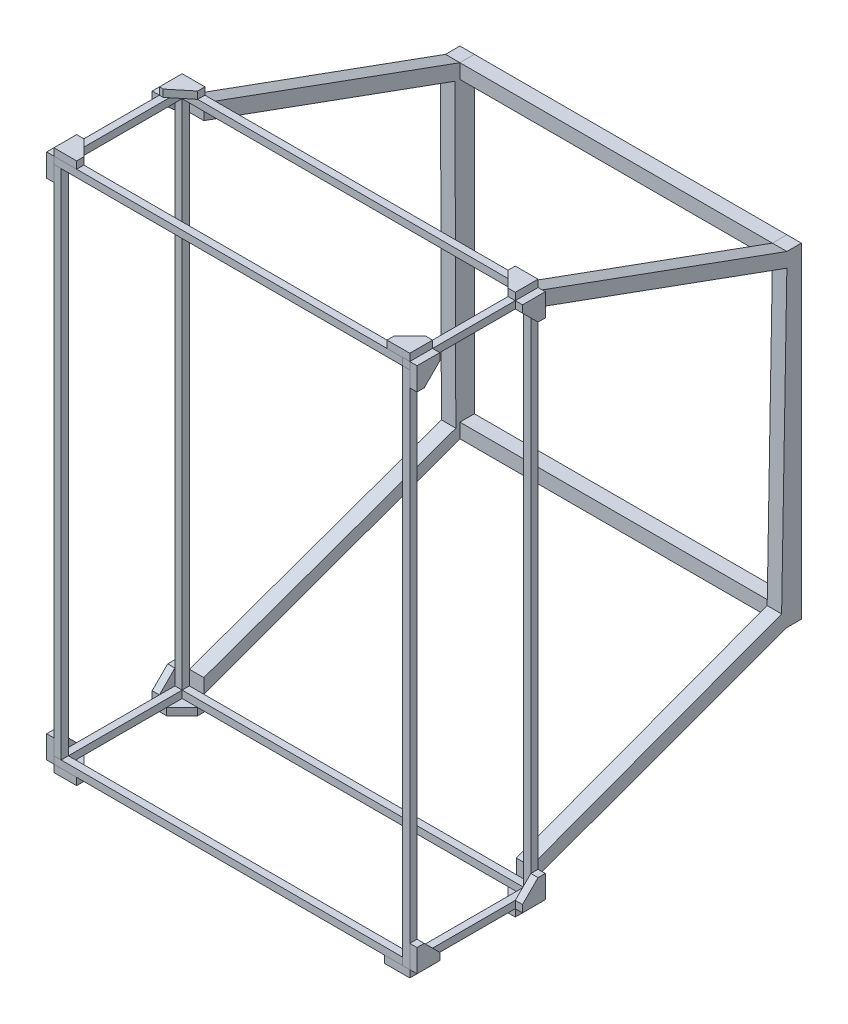
SolidWorks part; units mm, degrees
ref_plane "Front Plane" through (0, 0, 0) normal (0, 0, 1) x (1, 0, 0)
ref_plane "Top Plane" through (0, 0, 0) normal (0, 1, 0) x (1, 0, 0)
ref_plane "Right Plane" through (0, 0, 0) normal (1, 0, 0) x (0, 0, -1)
sketch "Sketch1" plane through (0, 0, 0) normal (0, 0, 1) x (1, 0, 0)
  line L1 (0, 0) -> (6.35, 0)
  line L2 (0, 0) -> (0, 6.35)
  line L3 (0, 6.35) -> (6.35, 6.35)
  line L4 (6.35, 0) -> (6.35, 6.35)
  dimension "D1" = 6.35
  dimension "D2" = 6.35
extrude "Boss-Extrude1" add sketch "Sketch1" along normal blind 100 contours L3 L4 L1 L2
ref_plane "Plane1" through (0, 0, 100) normal (1, 0, 0) x (0, 0, -1)
sketch "Sketch4" plane through (0, 0, 0) normal (0, -1, 0) x (-1, 0, 0)
  line L1 (0, -106.35) -> (-6.35, -106.35)
  line L2 (0, -106.35) -> (0, -100)
  line L3 (0, -100) -> (-6.35, -100)
  line L4 (-6.35, -106.35) -> (-6.35, -100)
  dimension "D1" = 6.35
extrude "Boss-Extrude3" add sketch "Sketch4" along normal blind 450 and the other way up to vertex (6.35 mm away) separate body contours L1 L4 L3 L2 other way up to point (0, 6.35, 100)
sketch "Sketch6" plane through (0, 0, 100) normal (0, 0, -1) x (-1, 0, 0)
  line L1 (-6.35, -450) -> (0, -450)
  line L2 (-6.35, -450) -> (-6.35, -456.3788)
  line L3 (-6.35, -456.3788) -> (0, -456.3788)
  line L4 (0, -450) -> (0, -456.3788)
extrude "Boss-Extrude4" add sketch "Sketch6" along normal blind 100 separate body contours L4 L3 L2 L1
sketch "Sketch7" plane through (6.35, 0, 0) normal (1, 0, 0) x (0, 0, -1)
  line L0 (-100, 0) -> (0, 0) construction
  line L1 (-106.35, 0) -> (-100, 0)
  line L2 (-106.35, 0) -> (-106.35, 6.35)
  line L3 (-106.35, 6.35) -> (-100, 6.35)
  line L4 (-100, 0) -> (-100, 6.35)
extrude "Boss-Extrude5" add sketch "Sketch7" along normal blind 300 and the other way up to vertex (6.35 mm away) separate body contours L3 L4 L1 L2 other way up to point (0, 6.35, 106.35)
sketch "Sketch8" plane through (6.35, 0, 0) normal (1, 0, 0) x (0, 0, -1)
  line L1 (-106.35, -450) -> (-100, -450)
  line L2 (-106.35, -450) -> (-106.35, -456.3788)
  line L3 (-106.35, -456.3788) -> (-100, -456.3788)
  line L4 (-100, -450) -> (-100, -456.3788)
extrude "Boss-Extrude6" add sketch "Sketch8" along normal blind 300 and the other way up to vertex (6.35 mm away) separate body other way up to point (0, -450, 106.35)
sketch "Sketch10" plane through (0, -450, 0) normal (0, 1, 0) x (1, 0, 0)
  line L1 (306.35, -100) -> (312.7, -100)
  line L2 (306.35, -100) -> (306.35, -106.35)
  line L3 (306.35, -106.35) -> (312.7, -106.35)
  line L4 (312.7, -100) -> (312.7, -106.35)
  dimension "D1" = 6.35
  dimension "D2" = 6.35
extrude "Boss-Extrude7" add sketch "Sketch10" along normal blind 450 and the other way up to vertex (6.3788 mm away) separate body contours L1 L4 L3 L2 other way up to point (306.35, -456.3788, 106.35)
sketch "Sketch12" plane through (0, 0, 0) normal (0, -1, 0) x (-1, 0, 0)
  line L1 (0, 0) -> (-6.35, 0)
  line L2 (0, 0) -> (0, 6.35)
  line L3 (0, 6.35) -> (-6.35, 6.35)
  line L4 (-6.35, 0) -> (-6.35, 6.35)
  dimension "D1" = 6.35
  dimension "D2" = 6.35
extrude "Boss-Extrude8" add sketch "Sketch12" along normal blind 450 and the other way up to vertex (6.35 mm away) separate body contours L2 L3 L4 L1 other way up to point (0, 6.35, 0)
sketch "Sketch16" plane through (0, 0, 100) normal (0, 0, -1) x (-1, 0, 0)
  line L1 (-306.35, -450) -> (-312.7, -450)
  line L2 (-306.35, -450) -> (-306.35, -456.35)
  line L3 (-306.35, -456.35) -> (-312.7, -456.35)
  line L4 (-312.7, -450) -> (-312.7, -456.35)
  line L5 (-306.35, 0) -> (-312.7, 0)
  line L6 (-306.35, 0) -> (-306.35, 6.4147)
  line L7 (-306.35, 6.4147) -> (-312.7, 6.4147)
  line L8 (-312.7, 0) -> (-312.7, 6.4147)
  dimension "D1" = 6.35
  dimension "D2" = 6.35
extrude "Boss-Extrude9" add sketch "Sketch16" along normal blind 100 separate body contours L3 L4 L1 L2
ref_plane "Plane2" through (312.7, 0, 100) normal (1, 0, 0) x (0, 0, -1)
ref_plane "Plane3" through (312.7, 0, 100) normal (0, -1, 0) x (-1, 0, 0)
sketch "Sketch20" plane through (0, 0, 100) normal (0, 0, -1) x (-1, 0, 0)
  line L0 (-436.45, 0) -> (-188.95, 0) construction
  line L1 (-306.35, 6.35) -> (-312.7, 6.35)
  line L2 (-306.35, 6.35) -> (-306.35, 0)
  line L3 (-306.35, 0) -> (-312.7, 0)
  line L4 (-312.7, 6.35) -> (-312.7, 0)
  line L5 (-312.7, 1.7463) -> (-312.7, -1.7463) construction
extrude "Boss-Extrude10" add sketch "Sketch20" along normal blind 100 and the other way up to vertex (6.35 mm away) separate body contours L1 L4 L3 L2 other way up to point (306.35, 6.35, 106.35)
sketch "Sketch21" plane through (6.35, 0, 0) normal (1, 0, 0) x (0, 0, -1)
  line L0 (0, -450) -> (0, -456.3788) construction
  line L1 (6.35, -450) -> (0, -450)
  line L2 (6.35, -450) -> (6.35, -456.3788)
  line L3 (6.35, -456.3788) -> (0, -456.3788)
  line L4 (0, -450) -> (0, -456.3788)
extrude "Boss-Extrude11" add sketch "Sketch21" along normal blind 300 and the other way up to vertex (6.35 mm away) separate body contours L2 L3 L4 L1 other way up to point (0, -456.3788, 0)
sketch "Sketch22" plane through (0, -450, 0) normal (0, 1, 0) x (1, 0, 0)
  line L1 (312.7, 0) -> (306.35, 0)
  line L2 (312.7, 0) -> (312.7, 6.35)
  line L3 (312.7, 6.35) -> (306.35, 6.35)
  line L4 (306.35, 0) -> (306.35, 6.35)
extrude "Boss-Extrude12" add sketch "Sketch22" along normal blind 450 and the other way up to vertex (6.35 mm away) separate body other way up to point (312.7, -456.35, 0)
sketch "Sketch23" plane through (306.35, 0, 0) normal (-1, 0, 0) x (0, 0, 1)
  line L0 (0, 6.35) -> (0, 0) construction
  line L1 (-6.35, 0) -> (0, 0)
  line L2 (-6.35, 0) -> (-6.35, 6.35)
  line L3 (-6.35, 6.35) -> (0, 6.35)
  line L4 (0, 0) -> (0, 6.35)
extrude "Boss-Extrude13" add sketch "Sketch23" along normal blind 300 and the other way up to vertex (6.35 mm away) separate body other way up to point (312.7, 6.35, 0)
sketch "Sketch24" plane through (0, -456.35, 0) normal (0, -1, 0) x (1, 0, 0)
  line L0 (6.35, 0) -> (6.35, 100) construction
  line L1 (0, 0) -> (0, 100) construction
  line L2 (6.35, 0) -> (6.35, 100)
  line L3 (0, 0) -> (0, 100)
  line L8 (6.35, 100) -> (0, 100)
  line L9 (0, 100) -> (0, 0)
  line L10 (0, 0) -> (6.35, 0)
  line L11 (6.35, 0) -> (6.35, 100)
  line L12 (6.35, 100) -> (0, 100)
  line L13 (0, 100) -> (0, 0)
  line L14 (0, 0) -> (6.35, 0)
  line L15 (6.35, 0) -> (6.35, 100)
  dimension "D1" = 0
sketch "Sketch25" plane through (6.35, 0, 0) normal (1, 0, 0) x (0, 0, -1)
  line L0 (6.35, 0) -> (231.35, -81.8933)
  line L1 (231.35, -81.8933) -> (227.0063, -93.8274)
  line L2 (227.0063, -93.8274) -> (6.35, -13.5151)
  line L3 (6.35, -450) -> (6.35, 6.35) construction
  line L4 (6.35, -13.5151) -> (6.35, 0)
  dimension "D1" = 12.7
  dimension "D2" = 70
  dimension "D3" = 225
extrude "Boss-Extrude20" add sketch "Sketch25" along normal blind 12.7 separate body contours L2 L4 L0 L1
sketch "Sketch26" plane through (306.35, 0, 0) normal (-1, 0, 0) x (0, 0, 1)
  line L0 (-6.35, 0) -> (-231.35, -81.8933)
  line L1 (-231.35, -81.8933) -> (-231.35, -94.5933)
  line L2 (-231.35, -94.5933) -> (-6.35, -12.7)
  line L3 (-6.35, 0) -> (-6.35, -456.35) construction
  line L4 (-6.35, -12.7) -> (-6.35, 0)
  dimension "D1" = 12.7
  dimension "D2" = 12.7
  dimension "D3" = 70
  dimension "D4" = 225
extrude "Boss-Extrude21" add sketch "Sketch26" along normal blind 12.7 separate body
sketch "Sketch27" plane through (306.35, 0, 0) normal (-1, 0, 0) x (0, 0, 1)
  line L0 (-6.35, -450) -> (-231.35, -368.1067)
  line L1 (-231.35, -368.1067) -> (-226.7276, -355.4067)
  line L2 (-226.7276, -355.4067) -> (-6.35, -437.3)
  line L3 (-6.35, 0) -> (-6.35, -456.35) construction
  line L4 (-6.35, -437.3) -> (-6.35, -450)
  dimension "D1" = 12.7
  dimension "D2" = 12.7
  dimension "D3" = 70
  dimension "D4" = 225
extrude "Boss-Extrude22" add sketch "Sketch27" along normal blind 12.7 separate body
sketch "Sketch28" plane through (6.35, 0, 0) normal (1, 0, 0) x (0, 0, -1)
  line L0 (6.35, -450) -> (231.35, -368.1067)
  line L1 (231.35, -368.1067) -> (227.7608, -358.2453)
  line L2 (227.7608, -358.2453) -> (6.35, -437.3)
  line L3 (6.35, -450) -> (6.35, 6.35) construction
  line L4 (6.35, -437.3) -> (6.35, -450)
  dimension "D1" = 70
  dimension "D2" = 12.7
  dimension "D3" = 225
extrude "Boss-Extrude23" add sketch "Sketch28" along normal blind 12.7 separate body
sketch "Sketch29" plane through (306.35, 0, 0) normal (1, 0, 0) x (0, 0, -1)
  line L0 (231.35, -81.8933) -> (231.35, -94.5933)
  line L1 (231.35, -94.5933) -> (226.7276, -355.4067)
  line L2 (226.7276, -355.4067) -> (231.35, -368.1067)
  line L3 (231.35, -368.1067) -> (244.05, -368.1067)
  line L4 (244.05, -368.1067) -> (244.05, -81.8933)
  line L5 (244.05, -81.8933) -> (231.35, -81.8933)
  dimension "D1" = 12.7
extrude "Boss-Extrude24" add sketch "Sketch29" against normal blind 12.7
sketch "Sketch31" plane through (6.35, 0, 0) normal (-1, 0, 0) x (0, 0, 1)
  line L0 (-231.35, -81.8933) -> (-227.0063, -93.8274)
  line L1 (-231.35, -81.8933) -> (-227.0063, -93.8274) construction
  line L2 (-227.0063, -93.8274) -> (-227.7608, -358.2453)
  line L3 (-227.7608, -358.2453) -> (-231.35, -368.1067)
  line L4 (-231.35, -368.1067) -> (-244.05, -368.1067)
  line L5 (-244.05, -368.1067) -> (-244.05, -81.8933)
  line L6 (-244.05, -81.8933) -> (-231.35, -81.8933)
extrude "Boss-Extrude25" add sketch "Sketch31" against normal blind 12.7
ref_plane "Plane6" through (306.35, -456.3788, 106.35) normal (0, -1, 0) x (-1, 0, 0)
ref_plane "Plane7" through (306.35, -450, 0) normal (0, 0, 1) x (1, 0, 0)
ref_plane "Plane8" through (0, 6.35, 0) normal (0, 1, 0) x (1, 0, 0)
sketch3d "3DSketch1"
  line L0 (312.7, 6.35, 88.7901) -> (312.7, -18.9378, 106.35)
  line L1 (312.7, 6.35, 0) -> (312.7, 6.35, 106.35) construction
  line L2 (312.7, 0, 106.35) -> (312.7, -456.3788, 106.35) construction
  line L3 (312.7, -18.9378, 106.35) -> (312.7, 6.35, 106.35)
  line L4 (312.7, 6.35, 88.7901) -> (312.7, 6.35, 106.35)
sketch "Sketch32" plane through (312.7, 0, 0) normal (1, 0, 0) x (0, 0, -1)
  line L0 (-106.35, 6.35) -> (-106.35, -13.65)
  line L1 (-106.35, -18.9378) -> (-106.35, 6.35) construction
  line L2 (-106.35, -13.65) -> (-100, -13.65)
  line L3 (-100, -456.3788) -> (-100, 0) construction
  line L4 (-100, -13.65) -> (-86.35, 0)
  line L5 (-106.35, 0) -> (0, 0) construction
  line L6 (-86.35, 0) -> (-86.35, 6.35)
  line L7 (-106.35, 6.35) -> (0, 6.35) construction
  line L8 (-86.35, 6.35) -> (-106.35, 6.35)
  dimension "D1" = 20
  dimension "D2" = 20
extrude "Boss-Extrude29" add sketch "Sketch32" along normal blind 6.35 separate body
sketch "Sketch33" plane through (312.7, 0, 0) normal (1, 0, 0) x (0, 0, -1)
  line L0 (-106.35, -456.3788) -> (-106.35, -436.3788)
  line L1 (-106.35, -456.3788) -> (-106.35, 0) construction
  line L2 (-106.35, -436.3788) -> (-100, -436.3788)
  line L3 (-100, -456.3788) -> (-100, 0) construction
  line L4 (-100, -436.3788) -> (-86.35, -450)
  line L5 (0, -450) -> (-100, -450) construction
  line L6 (-86.35, -450) -> (-86.35, -456.35)
  line L7 (0, -456.35) -> (-100, -456.35) construction
  line L8 (-86.35, -456.35) -> (-106.35, -456.3788)
  dimension "D1" = 20
  dimension "D2" = 20
extrude "Boss-Extrude30" add sketch "Sketch33" along normal blind 6.35 separate body
sketch "Sketch34" plane through (312.7, 0, 0) normal (1, 0, 0) x (0, 0, -1)
  line L0 (6.35, 6.35) -> (-13.65, 6.35)
  line L1 (-106.35, 6.35) -> (0, 6.35) construction
  line L2 (-13.65, 6.35) -> (-13.65, 0)
  line L3 (-106.35, 0) -> (0, 0) construction
  line L4 (-13.65, 0) -> (0, -13.65)
  line L5 (0, -456.35) -> (0, 0) construction
  line L6 (0, -13.65) -> (6.35, -13.65)
  line L7 (6.35, -456.35) -> (6.35, 0) construction
  line L8 (6.35, -13.65) -> (6.35, 6.35)
  dimension "D1" = 20
  dimension "D2" = 20
extrude "Boss-Extrude31" add sketch "Sketch34" along normal blind 6.35 separate body
sketch "Sketch35" plane through (312.7, 0, 0) normal (1, 0, 0) x (0, 0, -1)
  line L0 (6.35, -456.35) -> (-13.65, -456.35)
  line L1 (0, -456.35) -> (-100, -456.35) construction
  line L2 (-13.65, -456.35) -> (-13.65, -450)
  line L3 (0, -450) -> (-100, -450) construction
  line L4 (-13.65, -450) -> (0, -436.35)
  line L5 (0, -456.35) -> (0, 0) construction
  line L6 (0, -436.35) -> (6.35, -436.35)
  line L7 (6.35, -456.35) -> (6.35, 0) construction
  line L8 (6.35, -436.35) -> (6.35, -456.35)
  dimension "D1" = 20
  dimension "D2" = 20
extrude "Boss-Extrude32" add sketch "Sketch35" along normal blind 6.35 separate body
sketch "Sketch36" plane through (0, 0, 0) normal (-1, 0, 0) x (0, 0, 1)
  line L0 (106.35, 6.35) -> (106.35, -13.65)
  line L1 (106.35, 6.35) -> (106.35, -450) construction
  line L2 (106.35, -13.65) -> (100, -13.65)
  line L3 (100, 6.35) -> (100, -450) construction
  line L4 (100, -13.65) -> (86.35, 0)
  line L5 (100, 0) -> (0, 0) construction
  line L6 (86.35, 0) -> (86.35, 6.35)
  line L7 (100, 6.35) -> (0, 6.35) construction
  line L8 (86.35, 6.35) -> (106.35, 6.35)
  dimension "D1" = 20
  dimension "D2" = 20
extrude "Boss-Extrude33" add sketch "Sketch36" along normal blind 6.35 separate body
ref_plane "Plane9" through (0, -450, 106.35) normal (0, -1, 0) x (-1, 0, 0)
sketch "Sketch38" plane through (0, 0, 0) normal (-1, 0, 0) x (0, 0, 1)
  line L1 (106.35, -456.3788) -> (106.35, -436.3788)
  line L2 (106.35, 6.35) -> (106.35, -450) construction
  line L3 (106.35, -436.3788) -> (100, -436.3788)
  line L4 (100, 6.35) -> (100, -450) construction
  line L5 (100, -436.3788) -> (86.35, -450)
  line L6 (0, -450) -> (100, -450) construction
  line L7 (86.35, -450) -> (86.35, -456.35)
  line L8 (0, -456.35) -> (100, -456.35) construction
  line L9 (86.35, -456.35) -> (106.35, -456.3788)
  dimension "D1" = 20
  dimension "D2" = 20
extrude "Boss-Extrude34" add sketch "Sketch38" along normal blind 6.35 separate body
sketch "Sketch39" plane through (0, 0, 0) normal (-1, 0, 0) x (0, 0, 1)
  line L0 (-6.35, 6.35) -> (13.65, 6.35)
  line L1 (100, 6.35) -> (0, 6.35) construction
  line L2 (13.65, 6.35) -> (13.65, 0)
  line L3 (100, 0) -> (0, 0) construction
  line L4 (13.65, 0) -> (-2.2479, -13.65)
  line L5 (-2.2479, -13.65) -> (-6.35, -13.65)
  line L6 (-6.35, 6.35) -> (-6.35, -450) construction
  line L7 (-6.35, -13.65) -> (-6.35, 6.35)
  dimension "D1" = 20
  dimension "D2" = 20
extrude "Boss-Extrude35" add sketch "Sketch39" along normal blind 6.35 separate body
sketch "Sketch40" plane through (0, 0, 0) normal (-1, 0, 0) x (0, 0, 1)
  line L0 (-6.35, -456.3788) -> (13.65, -456.35)
  line L1 (0, -456.35) -> (100, -456.35) construction
  line L2 (13.65, -456.35) -> (13.65, -450)
  line L3 (0, -450) -> (100, -450) construction
  line L4 (13.65, -450) -> (0, -436.3788)
  line L5 (0, 6.35) -> (0, -450) construction
  line L6 (0, -436.3788) -> (-6.35, -436.3788)
  line L7 (-6.35, 6.35) -> (-6.35, -450) construction
  line L8 (-6.35, -436.3788) -> (-6.35, -456.3788)
  dimension "D1" = 20
  dimension "D2" = 20
extrude "Boss-Extrude36" add sketch "Sketch40" along normal blind 6.35 separate body
sketch "Sketch41" plane through (0, -456.3788, 0) normal (0, -1, 0) x (1, 0, 0)
  line L0 (0, 106.35) -> (20, 106.35)
  line L1 (0, 106.35) -> (306.35, 106.35) construction
  line L2 (20, 106.35) -> (20, 100)
  line L3 (0, 100) -> (306.35, 100) construction
  line L4 (20, 100) -> (6.35, 86.35)
  line L5 (6.35, 0) -> (6.35, 100) construction
  line L6 (6.35, 86.35) -> (0, 86.35)
  line L7 (0, 0) -> (0, 100) construction
  line L8 (0, 86.35) -> (0, 106.35)
  line L9 (312.7, 106.35) -> (290.2798, 106.35)
  line L10 (290.2798, 106.35) -> (290.2798, 100)
  line L11 (290.2798, 100) -> (306.35, 83.9298)
  line L12 (306.35, 0) -> (306.35, 100) construction
  line L13 (306.35, 83.9298) -> (312.7, 83.9298)
  line L14 (312.7, 98.2537) -> (312.7, 101.7463) construction
  line L15 (312.7, 83.9298) -> (312.7, 106.35)
  line L16 (0, -6.35) -> (0, 13.65)
  line L17 (0, 13.65) -> (6.35, 13.65)
  line L18 (6.35, 13.65) -> (20, 0)
  line L19 (0, 0) -> (306.35, 0) construction
  line L20 (20, 0) -> (20, -6.35)
  line L21 (0, -6.35) -> (306.35, -6.35) construction
  line L22 (20, -6.35) -> (0, -6.35)
  line L23 (312.7, -6.35) -> (312.7, 13.65)
  line L24 (312.7, 0) -> (312.7, 100) construction
  line L25 (312.7, 13.65) -> (312.7, -6.35) construction
  line L26 (312.7, 13.65) -> (306.35, 13.65)
  line L27 (306.35, 13.65) -> (292.7, 0)
  line L28 (292.7, 0) -> (292.7, -6.35)
  line L29 (292.7, -6.35) -> (312.7, -6.35)
  dimension "D1" = 20
  dimension "D2" = 20
  dimension "D3" = 20
  dimension "D4" = 20
extrude "Boss-Extrude37" add sketch "Sketch41" along normal blind 6.35 separate body
sketch "Sketch42" plane through (0, 6.35, 0) normal (0, 1, 0) x (1, 0, 0)
  line L0 (0, 6.35) -> (20, 6.35)
  line L1 (312.7, 6.35) -> (6.35, 6.35) construction
  line L2 (20, 6.35) -> (20, 0)
  line L3 (312.7, 0) -> (6.35, 0) construction
  line L4 (20, 0) -> (3.3198, -13.65)
  line L5 (3.3198, -13.65) -> (0, -13.65)
  line L6 (0, -13.65) -> (0, 6.35)
  line L7 (0, -106.35) -> (0, -86.35)
  line L8 (0, -100) -> (0, 0) construction
  line L9 (0, -86.35) -> (6.35, -86.35)
  line L10 (6.35, -100) -> (6.35, 0) construction
  line L11 (6.35, -86.35) -> (20, -100)
  line L12 (0, -100) -> (306.35, -100) construction
  line L13 (20, -100) -> (20, -106.35)
  line L14 (0, -106.35) -> (306.35, -106.35) construction
  line L15 (20, -106.35) -> (0, -106.35)
  line L16 (312.7, -106.35) -> (312.7, -86.35)
  line L17 (312.7, -106.35) -> (312.7, 0) construction
  line L18 (312.7, -86.35) -> (306.35, -86.35)
  line L19 (306.35, -106.35) -> (306.35, 0) construction
  line L20 (306.35, -86.35) -> (292.7, -100)
  line L21 (292.7, -100) -> (292.7, -106.35)
  line L22 (292.7, -106.35) -> (312.7, -106.35)
  line L23 (312.7, 6.35) -> (292.7, 6.35)
  line L24 (292.7, 6.35) -> (292.7, 0)
  line L25 (292.7, 0) -> (306.35, -13.65)
  line L26 (306.35, -13.65) -> (312.7, -13.65)
  line L27 (312.7, -13.65) -> (312.7, 6.35)
  dimension "D1" = 20
  dimension "D2" = 20
  dimension "D3" = 20
  dimension "D4" = 20
  dimension "D5" = 20
  dimension "D6" = 20
extrude "Boss-Extrude38" add sketch "Sketch42" along normal blind 6.35 separate body
sketch "Sketch43" plane through (0, -368.1067, 0) normal (0, -1, 0) x (1, 0, 0)
  line L0 (19.05, -231.35) -> (293.65, -231.35)
  line L1 (293.65, -231.35) -> (293.65, -244.05)
  line L2 (293.65, -244.05) -> (19.05, -244.05)
  line L3 (19.05, -244.05) -> (19.05, -231.35)
extrude "Boss-Extrude40" add sketch "Sketch43" against normal blind 12.7 separate body
sketch "Sketch44" plane through (0, -81.8933, 0) normal (0, 1, 0) x (1, 0, 0)
  line L0 (19.05, 244.05) -> (293.65, 244.05)
  line L1 (293.65, 231.35) -> (19.05, 231.35)
  line L2 (19.05, 231.35) -> (19.05, 244.05)
  line L7 (306.35, 231.35) -> (306.35, 244.05)
  line L8 (306.35, 244.05) -> (293.65, 244.05)
  line L9 (293.65, 244.05) -> (293.65, 231.35)
  line L10 (293.65, 231.35) -> (306.35, 231.35)
  line L13 (293.65, 244.05) -> (293.65, 231.35)
  dimension "D1" = 0
extrude "Boss-Extrude41" add sketch "Sketch44" against normal blind 12.7 separate body
